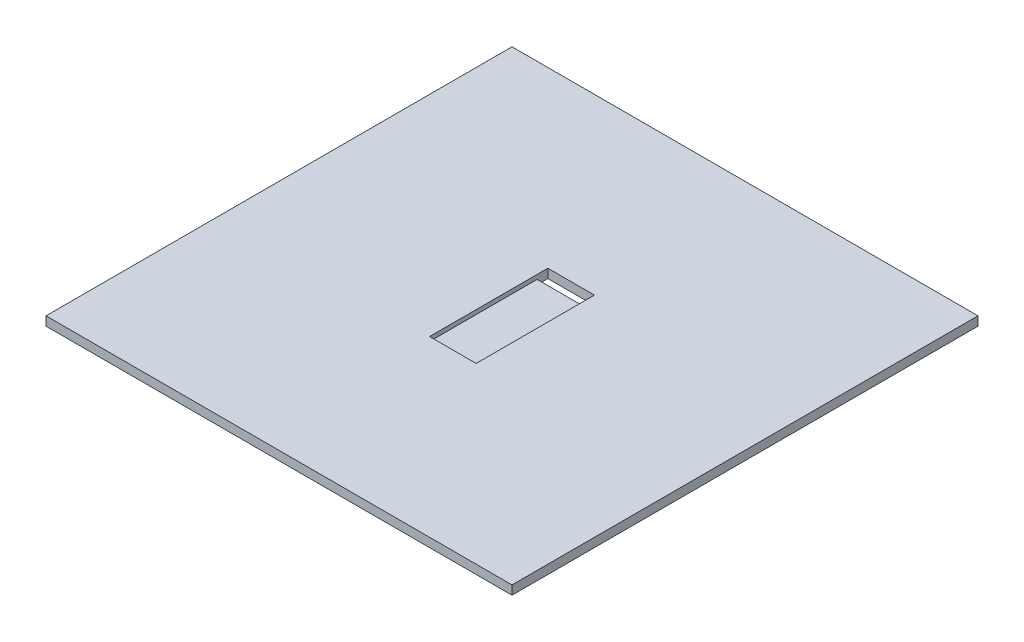
SolidWorks part; units mm, degrees
ref_plane "Front Plane" through (0, 0, 0) normal (0, 0, 1) x (1, 0, 0)
ref_plane "Top Plane" through (0, 0, 0) normal (0, 1, 0) x (1, 0, 0)
ref_plane "Right Plane" through (0, 0, 0) normal (1, 0, 0) x (0, 0, -1)
sketch "Sketch2" plane through (0, 0, 0) normal (0, 1, 0) x (1, 0, 0)
  line L1 (-65, -65) -> (65, -65)
  line L2 (-65, -65) -> (-65, 65)
  line L3 (-65, 65) -> (65, 65)
  line L4 (65, -65) -> (65, 65)
  line L5 (-65, -65) -> (65, 65) construction
  line L6 (-65, 65) -> (65, -65) construction
  point P0 (0, 0)
  dimension "D1" = 130
  dimension "D2" = 130
extrude "Boss-Extrude1" add sketch "Sketch2" along normal blind 2.5
sketch "Sketch3" plane through (0, 2.5, 0) normal (0, 1, 0) x (1, 0, 0)
  line L1 (-6.5, -16.5) -> (6.5, -16.5)
  line L2 (-6.5, -16.5) -> (-6.5, 16.5)
  line L3 (-6.5, 16.5) -> (6.5, 16.5)
  line L4 (6.5, -16.5) -> (6.5, 16.5)
  line L5 (-6.5, -16.5) -> (6.5, 16.5) construction
  line L6 (-6.5, 16.5) -> (6.5, -16.5) construction
  point P0 (0, 0)
  dimension "D1" = 13
  dimension "D2" = 33
extrude "Cut-Extrude1" cut sketch "Sketch3" against normal blind 1.2
sketch "Sketch4" plane through (0, 1.3, 0) normal (0, 1, 0) x (1, 0, 0)
  line L1 (-6.5, 13.5) -> (6.5, 13.5)
  line L2 (-6.5, 13.5) -> (-6.5, 16.5)
  line L3 (-6.5, 16.5) -> (6.5, 16.5)
  line L4 (6.5, 13.5) -> (6.5, 16.5)
  line L5 (-6.5, 13.5) -> (6.5, 16.5) construction
  line L6 (-6.5, 16.5) -> (6.5, 13.5) construction
  point P0 (0, 15)
  dimension "D1" = 13
  dimension "D2" = 3
extrude "Cut-Extrude2" cut sketch "Sketch4" against normal through all
